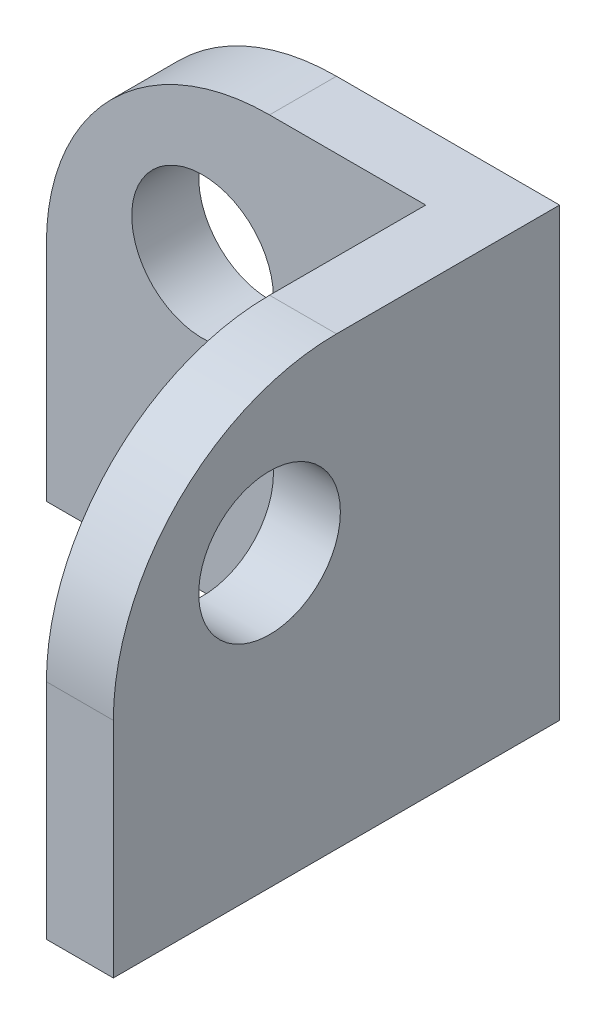
SolidWorks part; units mm, degrees
ref_plane "Front Plane" through (0, 0, 0) normal (0, 0, 1) x (1, 0, 0)
ref_plane "Top Plane" through (0, 0, 0) normal (0, 1, 0) x (1, 0, 0)
ref_plane "Right Plane" through (0, 0, 0) normal (1, 0, 0) x (0, 0, -1)
sketch "Sketch1" plane through (0, 0, 0) normal (0, 1, 0) x (1, 0, 0)
  line L0 (1.5, 1.5) -> (-1.5, -1.5) construction
  line L1 (-18.5, -1.5) -> (-1.5, -1.5)
  line L2 (-18.5, -1.5) -> (-18.5, 1.5)
  line L3 (-18.5, 1.5) -> (1.5, 1.5)
  line L6 (-1.5, -1.5) -> (-1.5, -18.5)
  line L7 (-1.5, -18.5) -> (1.5, -18.5)
  line L8 (1.5, 1.5) -> (1.5, -18.5)
  dimension "D1" = 20
  dimension "D2" = 3
extrude "Boss-Extrude1" add sketch "Sketch1" along normal blind 20
fillet "Fillet1" radius 10 2 edges at (-18.5, 20, 0) (0, 20, 18.5)
sketch "Sketch2" plane through (1.5, 0, 0) normal (1, 0, 0) x (0, 0, -1)
  line L0 (-18.5, 10) -> (-18.5, 0) construction
  line L1 (-8.5, 20) -> (1.5, 20) construction
  circle A0 centre (-11.5, 13) radius 3.175
  dimension "D1" = 6.35
  dimension "D2" = 7
  dimension "D3" = 7
extrude "Cut-Extrude1" cut sketch "Sketch2" against normal through all
sketch "Sketch3" plane through (0, 0, 1.5) normal (0, 0, 1) x (1, 0, 0)
  line L0 (-18.5, 10) -> (-18.5, 0) construction
  line L1 (-8.5, 20) -> (-1.5, 20) construction
  circle A0 centre (-11.5, 13) radius 3.175
  dimension "D1" = 6.35
  dimension "D2" = 7
  dimension "D3" = 7
extrude "Cut-Extrude2" cut sketch "Sketch3" against normal through all
